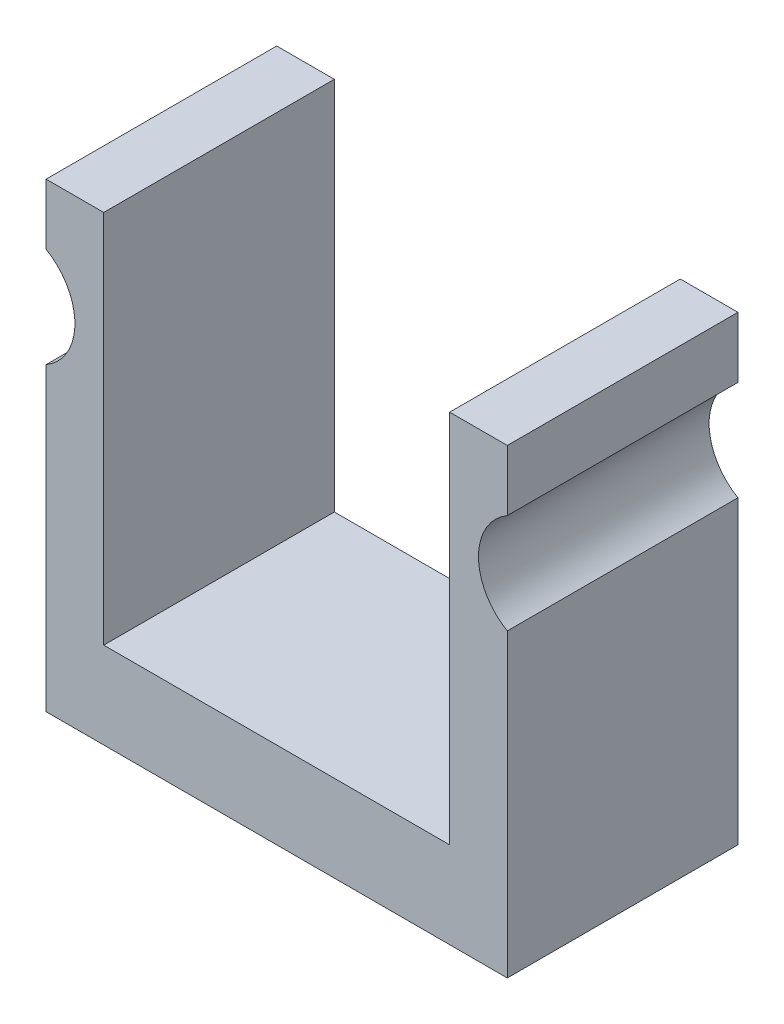
SolidWorks part; units mm, degrees
ref_plane "Front Plane" through (0, 0, 0) normal (0, 0, 1) x (1, 0, 0)
ref_plane "Top Plane" through (0, 0, 0) normal (0, 1, 0) x (1, 0, 0)
ref_plane "Right Plane" through (0, 0, 0) normal (1, 0, 0) x (0, 0, -1)
sketch "Sketch1" plane through (0, 0, 0) normal (0, 0, 1) x (1, 0, 0)
  line L0 (-34.0425, -19.3746) -> (16.7575, -19.3746)
  line L1 (16.7575, -19.3746) -> (16.7575, 31.4254)
  line L2 (16.7575, 31.4254) -> (10.4075, 31.4254)
  line L3 (10.4075, 31.4254) -> (10.4075, -9.8496)
  line L4 (10.4075, -9.8496) -> (-27.6925, -9.8496)
  line L5 (-27.6925, -9.8496) -> (-27.6925, 31.4254)
  line L6 (-34.0425, -19.3746) -> (-34.0425, 31.4254)
  line L7 (-34.0425, 31.4254) -> (-27.6925, 31.4254)
  dimension "D1" = 50.8
  dimension "D2" = 50.8
  dimension "D3" = 6.35
  dimension "D4" = 6.35
  dimension "D5" = 9.525
  dimension "D6" = 50.8
extrude "Boss-Extrude1" add sketch "Sketch1" along normal blind 25.4
sketch "Sketch2" plane through (0, 0, 25.4) normal (0, 0, 1) x (1, 0, 0)
  line L0 (-34.0425, 31.4254) -> (-34.0425, -19.3746) construction
  line L1 (-27.6925, 31.4254) -> (-34.0425, 31.4254) construction
  line L2 (16.7575, -19.3746) -> (16.7575, 31.4254) construction
  line L3 (16.7575, 31.4254) -> (10.4075, 31.4254) construction
  circle A0 centre (-37.2175, 19.2334) radius 6.35
  circle A1 centre (19.9325, 19.2334) radius 6.35
  point P12 (19.2614, 23.6331)
  dimension "D2" = 12.7
  dimension "D4" = 12.7
  dimension "D1" = 3.175
  dimension "D3" = 12.192
  dimension "D5" = 3.175
  dimension "D6" = 12.192
extrude "Cut-Extrude1" cut sketch "Sketch2" against normal blind 25.4
